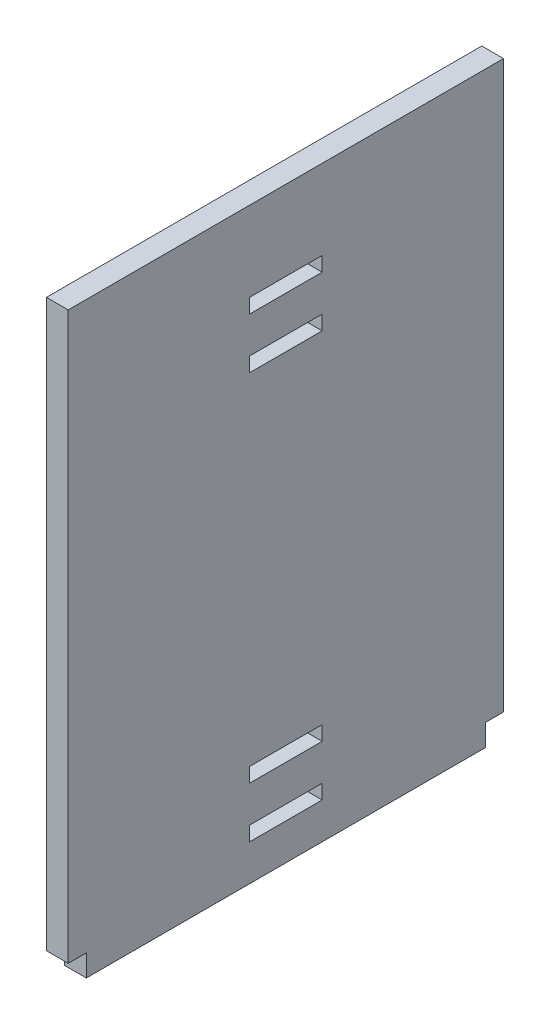
SolidWorks part; units mm, degrees
ref_plane "Alzado" through (0, 0, 0) normal (0, 0, 1) x (1, 0, 0)
ref_plane "Planta" through (0, 0, 0) normal (0, 1, 0) x (1, 0, 0)
ref_plane "Vista lateral" through (0, 0, 0) normal (1, 0, 0) x (0, 0, -1)
sketch "Croquis2" plane through (0, 0, 0) normal (1, 0, 0) x (0, 0, -1)
  line L1 (-67.5, 81) -> (67.5, 81)
  line L2 (-67.5, 81) -> (-67.5, -81)
  line L3 (-67.5, -81) -> (67.5, -81)
  line L4 (67.5, 81) -> (67.5, -81)
  line L5 (-67.5, 81) -> (67.5, -81) construction
  line L6 (-67.5, -81) -> (67.5, 81) construction
  point P0 (0, 0)
  dimension "D1" = 135
  dimension "D2" = 162
extrude "Saliente-Extruir1" add sketch "Croquis2" along normal blind 6
sketch "Croquis3" [suppressed] plane through (6, 0, 0) normal (1, 0, 0) x (0, 0, -1)
  line L0 (-47.5, -138.5106) -> (-47.5, -132.5106) construction
  line L1 (-67.5, -81) -> (-47.5, -81)
  line L2 (-67.5, -81) -> (-67.5, -75)
  line L3 (-67.5, -75) -> (-47.5, -75)
  line L4 (-47.5, -81) -> (-47.5, -75)
  line L5 (67.5, -81) -> (47.5, -81)
  line L6 (67.5, -81) -> (67.5, -75)
  line L7 (67.5, -75) -> (47.5, -75)
  line L8 (47.5, -81) -> (47.5, -75)
  dimension "D1" = 6
extrude "Cortar-Extruir1" [suppressed] cut sketch "Croquis3" against normal blind 6
sketch "Croquis4" plane through (0, 81, 0) normal (0, 1, 0) x (1, 0, 0)
  line L0 (0.025, 54) -> (5.975, 54) construction
  line L1 (6, 67.5) -> (0, 67.5)
  line L2 (6, 67.5) -> (6, 54)
  line L3 (6, 54) -> (0, 54)
  line L4 (0, 67.5) -> (0, 54)
  line L5 (6, 67.5) -> (6, -67.5) construction
  line L6 (0, -67.5) -> (6, -67.5)
  line L7 (0, -67.5) -> (0, -66)
  line L8 (0, -66) -> (6, -66)
  line L9 (6, -67.5) -> (6, -66)
  line L10 (0.025, -66) -> (5.975, -66) construction
  line L11 (0, 67.5) -> (0, -67.5) construction
extrude "Cortar-Extruir2" cut sketch "Croquis4" against normal through all
sketch "Croquis5" plane through (0, -81, 0) normal (0, -1, 0) x (1, 0, 0)
  line L0 (6, 66) -> (6, -54) construction
  line L1 (0, 67.5) -> (6, 67.5)
  line L2 (0, 67.5) -> (0, 61)
  line L3 (0, 61) -> (6, 61)
  line L4 (6, 67.5) -> (6, 61)
  line L5 (0.025, 61) -> (5.975, 61) construction
  line L7 (5.975, -49) -> (0.025, -49) construction
  line L8 (0, -54) -> (6, -54)
  line L9 (0, -54) -> (0, -49)
  line L10 (0, -49) -> (6, -49)
  line L11 (6, -54) -> (6, -49)
  point P4 (0, 0)
extrude "Cortar-Extruir3" cut sketch "Croquis5" against normal blind 6
sketch "Croquis6" [suppressed] plane through (6, 0, 0) normal (1, 0, 0) x (0, 0, -1)
  line L0 (0, 0) -> (0, -81) construction
  line L1 (-47.5, -81) -> (47.5, -81) construction
  line L2 (0, -17.3009) -> (0, -37.5725) construction
  line L3 (-10, -67) -> (10, -67)
  line L4 (-10, -67) -> (-10, -71)
  line L5 (-10, -71) -> (10, -71)
  line L6 (10, -67) -> (10, -71)
  line L7 (-10, -67) -> (10, -71) construction
  line L8 (-10, -71) -> (10, -67) construction
  line L14 (-10, -53) -> (-10, -57)
  line L19 (-10, -53) -> (10, -53)
  line L20 (10, -53) -> (10, -57)
  line L21 (-10, -57) -> (10, -57)
  line L22 (-10, -39) -> (-10, -43)
  line L23 (-10, -39) -> (10, -39)
  line L24 (10, -39) -> (10, -43)
  line L25 (-10, -43) -> (10, -43)
  line L26 (-10, -25) -> (-10, -29)
  line L27 (-10, -25) -> (10, -25)
  line L28 (10, -25) -> (10, -29)
  line L29 (-10, -29) -> (10, -29)
  line L30 (-10, -11) -> (-10, -15)
  line L31 (-10, -11) -> (10, -11)
  line L32 (10, -11) -> (10, -15)
  line L33 (-10, -15) -> (10, -15)
  line L34 (-10, 3) -> (-10, -1)
  line L35 (-10, 3) -> (10, 3)
  line L36 (10, 3) -> (10, -1)
  line L37 (-10, -1) -> (10, -1)
  line L38 (-10, 17) -> (-10, 13)
  line L39 (-10, 17) -> (10, 17)
  line L40 (10, 17) -> (10, 13)
  line L41 (-10, 13) -> (10, 13)
  line L42 (-10, 31) -> (-10, 27)
  line L43 (-10, 31) -> (10, 31)
  line L44 (10, 31) -> (10, 27)
  line L45 (-10, 27) -> (10, 27)
  line L46 (-10, 45) -> (-10, 41)
  line L47 (-10, 45) -> (10, 45)
  line L48 (10, 45) -> (10, 41)
  line L49 (-10, 41) -> (10, 41)
  line L50 (-10, 59) -> (-10, 55)
  line L51 (-10, 59) -> (10, 59)
  line L52 (10, 59) -> (10, 55)
  line L53 (-10, 55) -> (10, 55)
  point P5 (0, -69)
  dimension "D1" = 10
  dimension "D2" = 4
  dimension "D3" = 20
  dimension "D4" = 10
extrude "Cortar-Extruir4" [suppressed] cut sketch "Croquis6" against normal through all contours L50 L53 L52 L51 | L46 L49 L48 L47 | L42 L45 L44 L43 | L6 L3 L4 L5 | L14 L21 L20 L19 | L25 L24 L23 L22
sketch "Croquis7" plane through (6, 0, 0) normal (1, 0, 0) x (0, 0, -1)
  line L1 (-16, -71) -> (4, -71)
  line L2 (-16, -71) -> (-16, -67)
  line L3 (-16, -67) -> (4, -67)
  line L4 (4, -71) -> (4, -67)
  line L5 (-16, -57) -> (4, -57)
  line L6 (-16, -57) -> (-16, -53)
  line L7 (-16, -53) -> (4, -53)
  line L8 (4, -57) -> (4, -53)
  line L17 (-16, 41) -> (4, 41)
  line L18 (-16, 41) -> (-16, 45)
  line L19 (-16, 45) -> (4, 45)
  line L20 (4, 41) -> (4, 45)
  line L21 (-16, 55) -> (4, 55)
  line L22 (-16, 55) -> (-16, 59)
  line L23 (-16, 59) -> (4, 59)
  line L24 (4, 55) -> (4, 59)
extrude "Cortar-Extruir5" cut sketch "Croquis7" against normal blind 6
